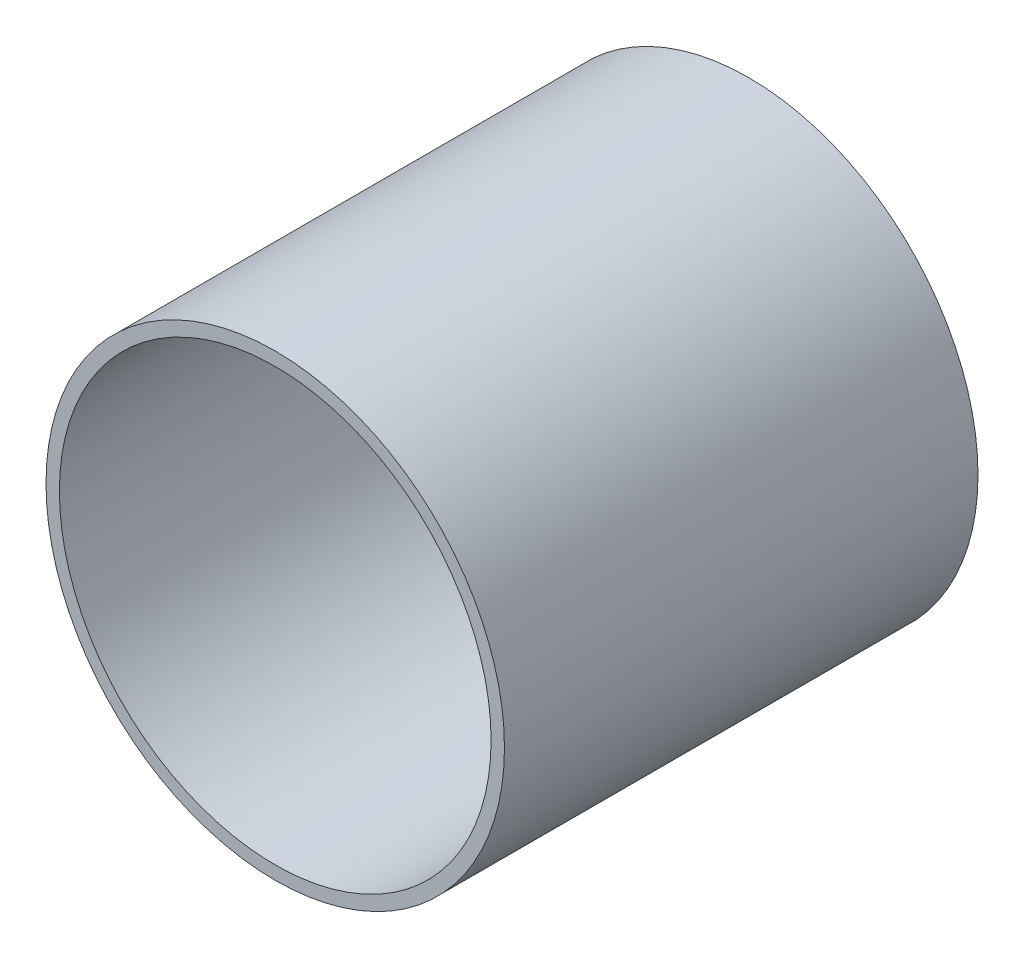
SolidWorks part; units mm, degrees
material "Silicon Rubber"
ref_plane "Front Plane" through (0, 0, 0) normal (0, 0, 1) x (1, 0, 0)
ref_plane "Top Plane" through (0, 0, 0) normal (0, 1, 0) x (1, 0, 0)
ref_plane "Right Plane" through (0, 0, 0) normal (1, 0, 0) x (0, 0, -1)
sketch "Sketch1" plane through (0, 0, 0) normal (0, 0, 1) x (1, 0, 0)
  circle A0 centre (0, 0) radius 32.25
  circle A1 centre (0, 0) radius 34.25
  circle A2 centre (0, 0) radius 32.25 construction
  dimension "D1" = 2
extrude "Boss-Extrude1" add sketch "Sketch1" along normal up to surface (70.75 mm away)
